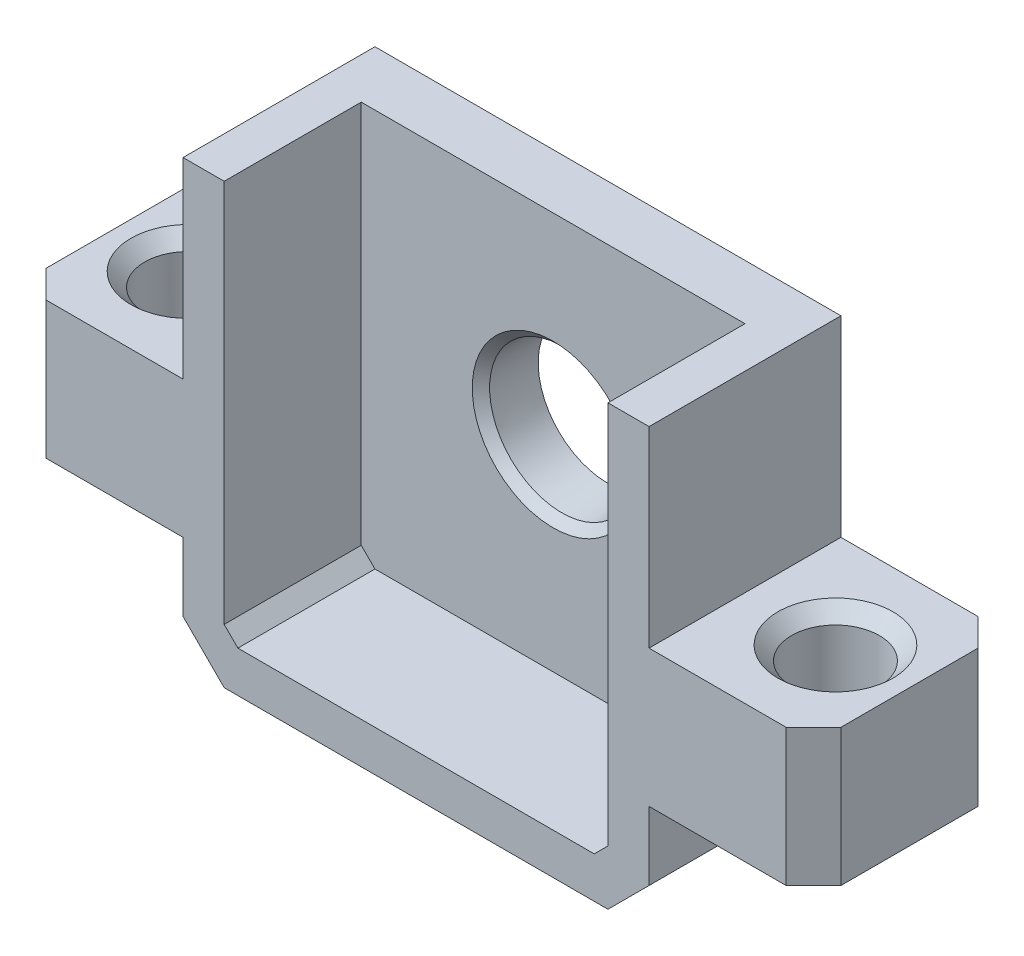
SolidWorks part; units mm, degrees
ref_plane "Plan de face" through (0, 0, 0) normal (0, 0, 1) x (1, 0, 0)
ref_plane "Plan de dessus" through (0, 0, 0) normal (0, 1, 0) x (1, 0, 0)
ref_plane "Plan de droite" through (0, 0, 0) normal (1, 0, 0) x (0, 0, -1)
sketch "Esquisse1" plane through (0, 0, 0) normal (0, 0, 1) x (1, 0, 0)
  line L0 (-8.5, 9) -> (8.5, -9) construction
  line L1 (-8.5, 9) -> (8.5, 9)
  line L2 (-8.5, 9) -> (-8.5, -9)
  line L3 (-8.5, -9) -> (8.5, -9)
  line L4 (8.5, 9) -> (8.5, -9)
  dimension "D1" = 18
  dimension "17" = 17
extrude "Boss.-Extru.1" add sketch "Esquisse1" along normal blind 2
sketch "Esquisse2" plane through (0, 0, 2) normal (0, 0, 1) x (1, 0, 0)
  line L0 (-8.5, -9) -> (8.5, -9) construction
  line L1 (-8.5, 9) -> (8.5, 9)
  line L2 (-8.5, 9) -> (-8.5, -9)
  line L3 (-8.5, -9) -> (8.5, -9)
  line L4 (8.5, 9) -> (8.5, -9)
  line L5 (-7, 7.5) -> (7, -7.5) construction
  line L6 (-7, 7.5) -> (7, 7.5)
  line L7 (-7, 7.5) -> (-7, -7.5)
  line L8 (-7, -7.5) -> (7, -7.5)
  line L9 (7, 7.5) -> (7, -7.5)
  line L10 (8.5, -9) -> (8.5, 9) construction
  dimension "D1" = 1.5
  dimension "D2" = 1.5
extrude "Boss.-Extru.2" add sketch "Esquisse2" along normal blind 5
sketch "Esquisse3" plane through (-8.5, 0, 0) normal (-1, 0, 0) x (0, 0, 1)
  line L0 (0, 9) -> (0, -9) construction
  line L1 (0, 0) -> (7, 0)
  line L2 (0, 0) -> (0, -5)
  line L3 (0, -5) -> (7, -5)
  line L4 (7, 0) -> (7, -5)
  line L5 (7, 9) -> (7, -9) construction
  dimension "D1" = 5
extrude "Boss.-Extru.3" add sketch "Esquisse3" along normal blind 6
sketch "Esquisse4" plane through (0, 0, 0) normal (0, 1, 0) x (1, 0, 0)
  line L0 (-8.5, -7) -> (-8.5, 0) construction
  circle A0 centre (-11.8, -3.5) radius 1.6
  dimension "D1" = 3.2
  dimension "D2" = 3.3
extrude "Enlèv. mat.-Extru.1" cut sketch "Esquisse4" against normal through all
chamfer "Chanfrein1" distance 1 angle 45 2 edges at (-14.5, -2.5, 0) (-14.5, -2.5, 7)
mirror "Symétrie2" about plane through (0, 0, 0) normal (1, 0, 0) of "Chanfrein1", "Boss.-Extru.3", "Enlèv. mat.-Extru.1"
chamfer "Chanfrein2" distance 1.5 angle 45 4 edges at (-8.5, 9, 3.5) (8.5, 9, 3.5) (8.5, -9, 3.5) (-8.5, -9, 3.5)
chamfer "Chanfrein3" distance 0.5 angle 45 4 edges at (7, -7.5, 4.5) (7, 7.5, 4.5) (-7, 7.5, 4.5) (-7, -7.5, 4.5)
sketch "Esquisse5" plane through (0, 0, 2) normal (0, 0, 1) x (1, 0, 0)
  circle A0 centre (0, 0) radius 2.65
  dimension "D1" = 5.3
extrude "Enlèv. mat.-Extru.2" cut sketch "Esquisse5" against normal blind 2 draft 3
chamfer "Chanfrein4" distance 0.3 angle 45 1 edges at (2.65, 0, 2)
chamfer "Chanfrein5" distance 0.5 angle 45 2 edges at (11.8, 0, 5.1) (-11.8, 0, 5.1)
sketch "Esquisse6" plane through (0, 9, 0) normal (0, 1, 0) x (1, 0, 0)
  line L1 (-10.838, 2.3835) -> (14.4556, 2.3835)
  line L2 (-10.838, 2.3835) -> (-10.838, -10.7472)
  line L3 (-10.838, -10.7472) -> (14.4556, -10.7472)
  line L4 (14.4556, 2.3835) -> (14.4556, -10.7472)
extrude "Enlèv. mat.-Extru.3" cut sketch "Esquisse6" against normal blind 2
